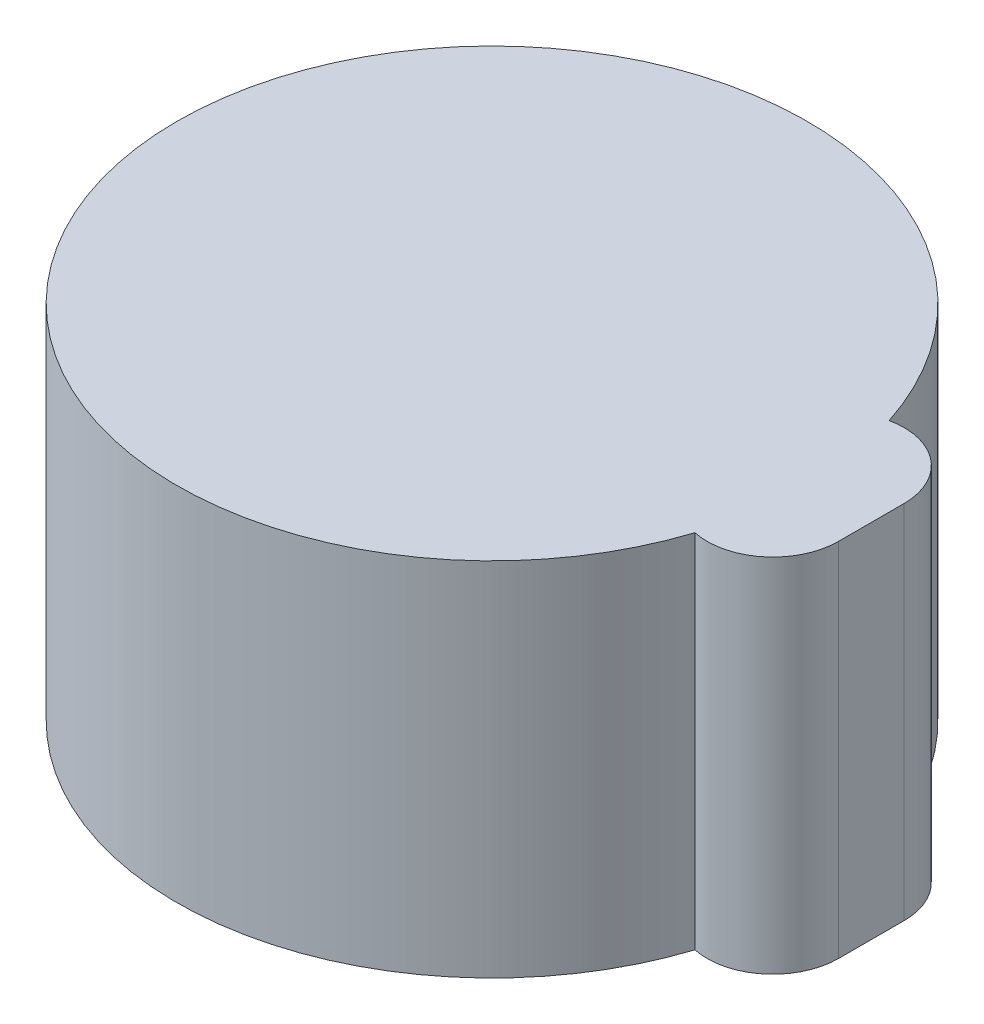
SolidWorks part; units mm, degrees
ref_plane "Front Plane" through (0, 0, 0) normal (0, 0, 1) x (1, 0, 0)
ref_plane "Top Plane" through (0, 0, 0) normal (0, 1, 0) x (1, 0, 0)
ref_plane "Right Plane" through (0, 0, 0) normal (1, 0, 0) x (0, 0, -1)
sketch "Sketch1" plane through (0, 0, 0) normal (0, 1, 0) x (1, 0, 0)
  line L0 (-6.6188, 0) -> (7.2814, 0) construction
  line L1 (5.2739, 0.5) -> (5.7739, 0.5) construction
  line L2 (0, 4.3) -> (0, 4.8) construction
  line L3 (5.7739, 0.5) -> (5.7739, -0.5)
  line L4 (4.696, 0.9939) -> (4.1836, 0.9939)
  line L5 (4.696, -0.9939) -> (4.1836, -0.9939)
  line L6 (5.2739, 0.5) -> (5.2739, -0.5)
  circle A0 centre (0, 0) radius 4.3
  circle A1 centre (0, 0) radius 4.8
  circle A2 centre (4.7739, 0.5) radius 0.5
  circle A3 centre (4.7739, -0.5) radius 0.5
  circle A4 centre (4.7739, 0.5) radius 1
  circle A5 centre (4.7739, -0.5) radius 1
  dimension "D1" = 8.6
  dimension "D2" = 0.5
  dimension "D3" = 1
extrude "Boss-Extrude1" add sketch "Sketch1" along normal blind 5
sketch "Sketch3" plane through (0, 5, 0) normal (0, 1, 0) x (1, 0, 0)
  line L1 (5.7739, -0.5) -> (5.7739, 0.5)
  line L2 (5.7739, -0.5) -> (5.7739, 0.5)
  arc A3 (4.5667, -1.4783) -> (5.7739, -0.5) centre (4.7739, -0.5) ccw
  arc A4 (5.7739, 0.5) -> (4.5667, 1.4783) centre (4.7739, 0.5) ccw
  arc A5 (4.5667, 1.4783) -> (4.5667, -1.4783) centre (0, 0) ccw
  arc A6 (4.5667, -1.4783) -> (5.7739, -0.5) centre (4.7739, -0.5) ccw
  arc A7 (5.7739, 0.5) -> (4.5667, 1.4783) centre (4.7739, 0.5) ccw
  arc A8 (4.5667, 1.4783) -> (4.5667, -1.4783) centre (0, 0) ccw
  dimension "D1" = 0
extrude "Boss-Extrude2" add sketch "Sketch3" along normal blind 0.5
sketch "Sketch4" plane through (0, 5, 0) normal (0, -1, 0) x (1, 0, 0)
  line L0 (4.1836, 0.9939) -> (3.6677, 0.9939)
  line L1 (4.1836, -0.9939) -> (3.6677, -0.9939)
  circle A0 centre (0, 0) radius 3.8
  arc A1 (4.1836, 0.9939) -> (4.1836, -0.9939) centre (0, 0) ccw construction
  dimension "D1" = 0.5
extrude "Boss-Extrude3" add sketch "Sketch4" along normal blind 1
sketch "Sketch5" plane through (0, 4, 0) normal (0, -1, 0) x (1, 0, 0)
  line L0 (0, 4.3) -> (0, -4.3) construction
  line L1 (3.0406, -3.0406) -> (-3.0406, 3.0406) construction
  line L2 (-3.0406, -3.0406) -> (3.0406, 3.0406) construction
  arc A0 (4.1836, 0.9939) -> (4.1836, -0.9939) centre (0, 0) ccw construction
  arc A1 (4.1836, 0.9939) -> (4.1836, -0.9939) centre (0, 0) ccw construction
  circle A2 centre (3.0406, 3.0406) radius 0.25
  circle A3 centre (-3.0406, 3.0406) radius 0.25
  circle A4 centre (-3.0406, -3.0406) radius 0.25
  circle A5 centre (3.0406, -3.0406) radius 0.25
  dimension "D2" = 0.5
  dimension "D1" = 45
extrude "Boss-Extrude4" [suppressed] add sketch "Sketch5" along normal up to surface (4 mm away)
